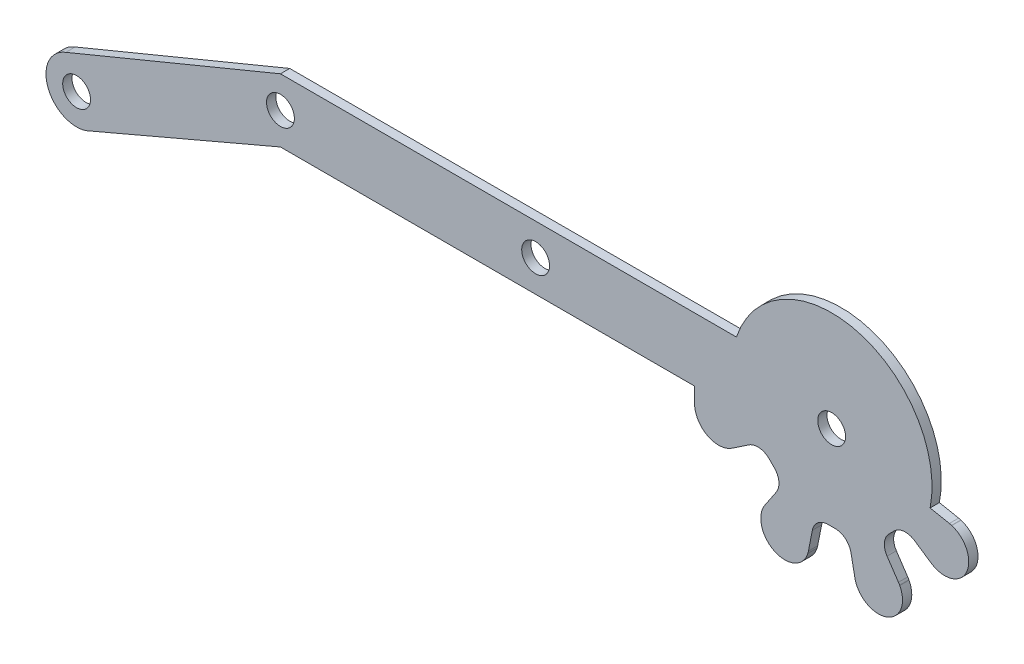
SolidWorks part; units mm, degrees
ref_plane "Alzado" through (0, 0, 0) normal (0, 0, 1) x (1, 0, 0)
ref_plane "Planta" through (0, 0, 0) normal (0, 1, 0) x (1, 0, 0)
ref_plane "Vista lateral" through (0, 0, 0) normal (1, 0, 0) x (0, 0, -1)
sketch "Model" plane through (0, 0, 0) normal (0, 0, 1) x (1, 0, 0)
  line L0 (6.2612, 18.7694) -> (-14.7395, 9.795)
  line L1 (-16.8722, 16.0373) -> (6.2612, 25.6004)
  line L2 (6.2612, 25.6004) -> (33.7612, 25.6004)
  line L3 (33.7612, 25.6004) -> (55.3989, 25.6004)
  line L4 (76.2718, 20.0884) -> (78.3467, 19.6785)
  line L5 (78.5802, 19.621) -> (78.6119, 19.6114)
  line L6 (76.6385, 14.8471) -> (76.6093, 14.8627)
  line L7 (76.4035, 14.9871) -> (74.5751, 16.2122)
  line L8 (72.351, 15.9546) -> (71.8915, 15.4951)
  line L9 (71.6339, 13.271) -> (72.859, 11.4426)
  line L10 (72.9834, 11.2368) -> (72.999, 11.2076)
  line L11 (68.2347, 9.2342) -> (68.2251, 9.2659)
  line L12 (68.1676, 9.4994) -> (67.741, 11.6585)
  line L13 (65.9861, 13.049) -> (65.3363, 13.049)
  line L14 (63.5814, 11.6585) -> (63.1548, 9.4994)
  line L15 (63.0973, 9.2659) -> (63.0877, 9.2342)
  line L16 (58.3234, 11.2076) -> (58.339, 11.2368)
  line L17 (58.4635, 11.4426) -> (59.6886, 13.271)
  line L18 (59.431, 15.4951) -> (58.9715, 15.9546)
  line L19 (56.7473, 16.2122) -> (54.9189, 14.9871)
  line L20 (54.7132, 14.8627) -> (54.6839, 14.8471)
  line L21 (50.8883, 17.1382) -> (50.8883, 18.7694)
  line L22 (50.8883, 18.7694) -> (6.2612, 18.7694)
  circle A0 centre (65.6612, 22.1849) radius 1.5
  arc A1 (-16.8722, 16.0373) -> (-14.7395, 9.795) centre (-15.7058, 12.9504) ccw
  arc A2 (76.2718, 20.0884) -> (55.3989, 25.6004) centre (65.6612, 22.1849) ccw
  arc A3 (78.5802, 19.621) -> (78.3467, 19.6785) centre (77.8448, 17.1382) ccw
  arc A4 (76.6385, 14.8471) -> (78.6119, 19.6114) centre (77.8448, 17.1382) ccw
  arc A5 (76.4035, 14.9871) -> (76.6093, 14.8627) centre (77.8448, 17.1382) ccw
  arc A6 (74.5751, 16.2122) -> (72.351, 15.9546) centre (73.6142, 14.7781) ccw
  arc A7 (71.8915, 15.4951) -> (71.6339, 13.271) centre (73.0679, 14.2319) ccw
  arc A8 (72.9834, 11.2368) -> (72.859, 11.4426) centre (70.7078, 10.0012) ccw
  arc A9 (68.2347, 9.2342) -> (72.999, 11.2076) centre (70.7078, 10.0012) ccw
  arc A10 (68.1676, 9.4994) -> (68.2251, 9.2659) centre (70.7078, 10.0012) ccw
  arc A11 (67.741, 11.6585) -> (65.9861, 13.049) centre (66.0475, 11.3239) ccw
  arc A12 (65.3363, 13.049) -> (63.5814, 11.6585) centre (65.2749, 11.3239) ccw
  arc A13 (63.0973, 9.2659) -> (63.1548, 9.4994) centre (60.6146, 10.0012) ccw
  arc A14 (58.3234, 11.2076) -> (63.0877, 9.2342) centre (60.6146, 10.0012) ccw
  arc A15 (58.4635, 11.4426) -> (58.339, 11.2368) centre (60.6146, 10.0012) ccw
  arc A16 (59.6886, 13.271) -> (59.431, 15.4951) centre (58.2545, 14.2319) ccw
  arc A17 (58.9715, 15.9546) -> (56.7473, 16.2122) centre (57.7082, 14.7781) ccw
  arc A18 (54.7132, 14.8627) -> (54.9189, 14.9871) centre (53.4776, 17.1382) ccw
  arc A19 (50.8883, 17.1382) -> (54.6839, 14.8471) centre (53.4776, 17.1382) ccw
  circle A20 centre (33.7612, 22.1849) radius 1.5
  circle A21 centre (6.2612, 22.1849) radius 1.5
  circle A22 centre (-15.7058, 12.9504) radius 1.5
extrude "Saliente-Extruir1" add sketch "Model" along normal blind 1
